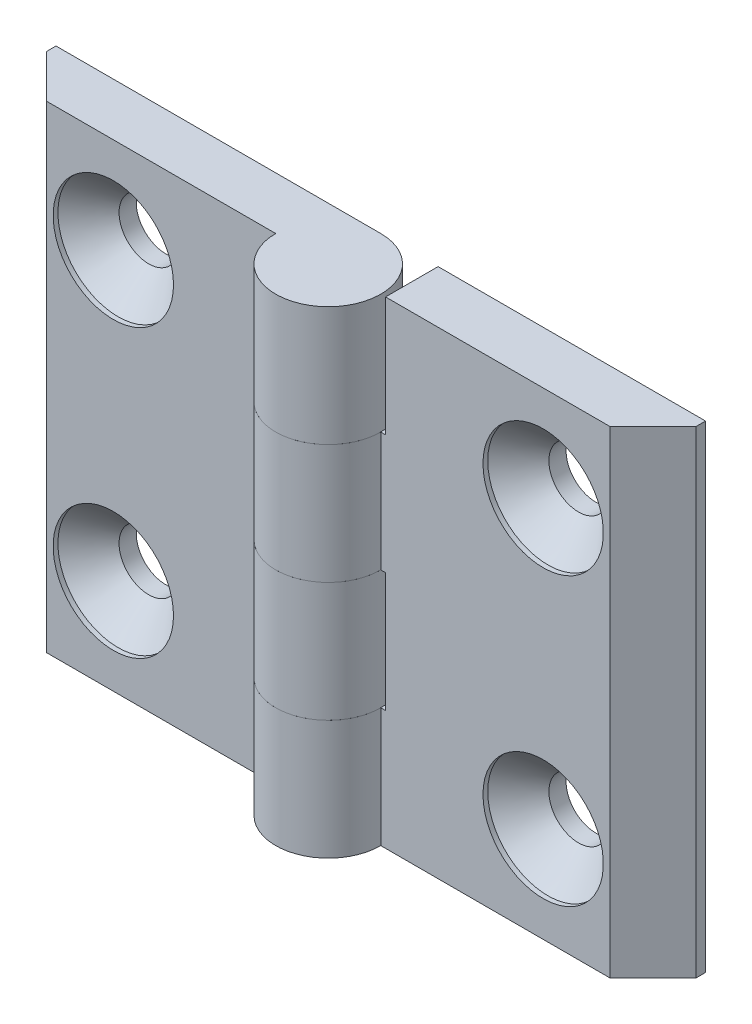
SolidWorks part; units mm, degrees
material "Алюминиевый сплав"
ref_plane "Спереди" through (0, 0, 0) normal (0, 0, 1) x (1, 0, 0)
ref_plane "Сверху" through (0, 0, 0) normal (0, 1, 0) x (1, 0, 0)
ref_plane "Справа" through (0, 0, 0) normal (1, 0, 0) x (0, 0, -1)
sketch "Эскиз1" plane through (0, 0, 0) normal (0, 1, 0) x (1, 0, 0)
  line L0 (0, 5.5) -> (-34, 5.5)
  line L1 (-34, 5.5) -> (-34, 4.5)
  line L2 (-34, 4.5) -> (-29.5, 0)
  line L3 (-29.5, 0) -> (-5.5, 0)
  line L4 (0, 0) -> (0, 10.5526) construction
  arc A0 (-5.5, 0) -> (0, 5.5) centre (0, 0) ccw
  dimension "D1" = 68
  dimension "D2" = 5.5
  dimension "D3" = 1
  dimension "D4" = 45
extrude "Бобышка-Вытянуть1" add sketch "Эскиз1" along normal mid plane 50
sketch "Эскиз3" plane through (0, 0, 0) normal (0, 0, 1) x (1, 0, 0)
  line L0 (5.5, -25) -> (5.5, 25) construction
  line L1 (-6, 12.5) -> (5.5, 12.5)
  line L2 (-6, 12.5) -> (-6, 0)
  line L3 (-6, 0) -> (5.5, 0)
  line L4 (5.5, 12.5) -> (5.5, 0)
  line L5 (5.5, 0) -> (5.5, -12.5) construction
  line L6 (5.5, -25) -> (-6, -25)
  line L7 (5.5, -25) -> (5.5, -12.5)
  line L8 (5.5, -12.5) -> (-6, -12.5)
  line L9 (-6, -25) -> (-6, -12.5)
  line L10 (5.5, 12.5) -> (5.5, 25) construction
  line L11 (-5.5, 25) -> (-5.5, -25) construction
  dimension "D1" = 0.5
extrude "Вырез-Вытянуть1" cut sketch "Эскиз3" against normal through all and the other way through all
hole_wizard "Зенковка для винта с полупотайной головкой M61" positions "Эскиз4" profile "Эскиз6" countersink size "M6" standard "ISO" end condition through all
sketch "Эскиз4" plane through (0, 0, 0) normal (0, 0, 1) x (1, 0, 0)
  line L0 (-22.5, 15) -> (-22.5, -15)
  line L2 (0, 0) -> (0, 18.9001) construction
  line L3 (5.5, 0) -> (-5.5, 0) construction
  point P0 (-22.5, 15)
  point P2 (-22.5, -15)
  point P9 (-22.5, 0)
  dimension "D1" = 30
  dimension "D2" = 45
sketch "Эскиз6" plane through (-22.5, 15, 0) normal (1, 0, 0) x (0, -1, 0)
  line L0 (0, 0) -> (0, 5.5)
  line L1 (0, 5.5) -> (3.1, 5.5)
  line L2 (3.1, 5.5) -> (3.1, 3.7)
  line L3 (3.1, 3.7) -> (6.3, 0.5)
  line L4 (6.3, 0.5) -> (6.3, 0)
  line L6 (6.3, 0) -> (0, 0)
  line L7 (-3.1, 3.7) -> (-6.3, 0.5) construction
  line L11 (0, -6.35) -> (0, 107.95) construction
  dimension "Диаметр сквозного отверстия" = 6.2
  dimension "Глубина сквозного отверстия" = 5.5
  dimension "Диаметр зенковки" = 12.6
  dimension "Угол зенковки" = 90
  dimension "Утопленность" = 0.5
sketch "Угол раскрытия" plane through (0, 0, 0) normal (0, 1, 0) x (1, 0, 0)
  line L0 (0, 0) -> (0, -10)
  line L7 (0, 5.5) -> (-34, 5.5) construction
  point P3 (-11.2006, -8.7746)
  point P8 (-7.4924, -9.3736)
  point P9 (0, 0)
  point P10 (-11.8016, -2.1731)
  dimension "D1" = 10
  dimension "D2" = 90
pattern_circular "Круговой массив1" count 2 over 360 about axis through (0, 0, 0) along (0, 0, 1) of bodies 106
